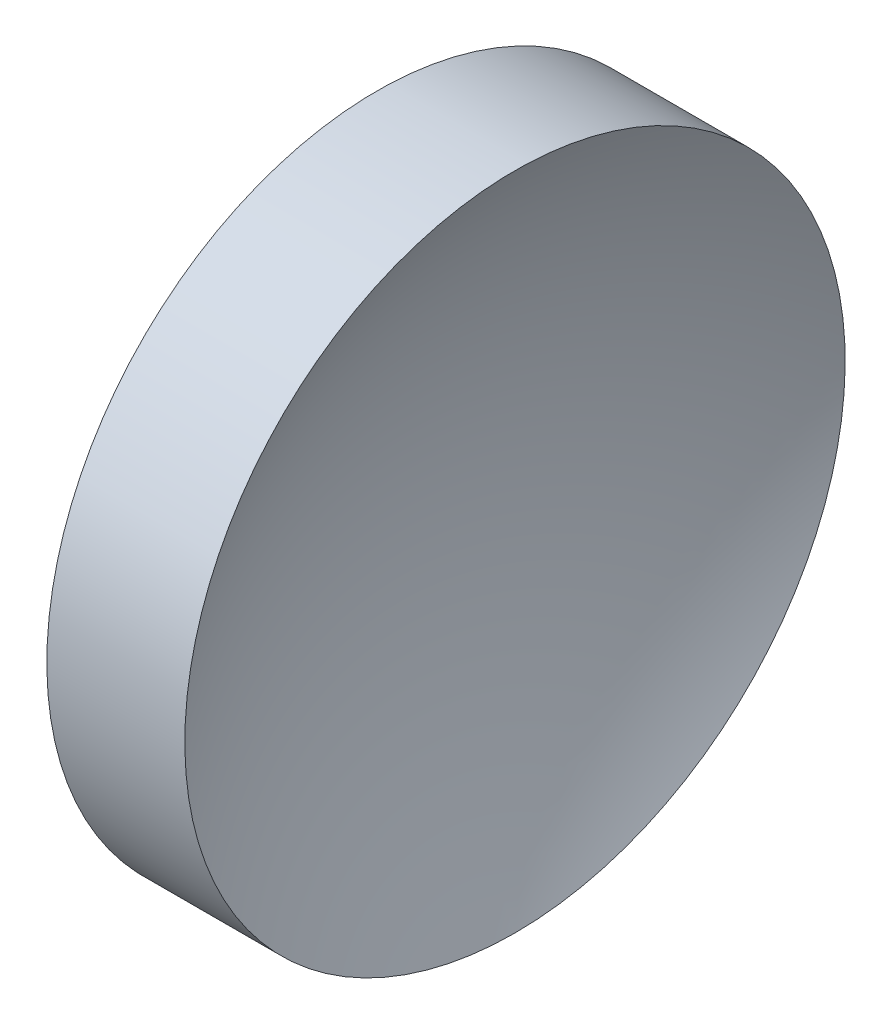
SolidWorks part; units mm, degrees
ref_plane "前视基准面" through (0, 0, 0) normal (0, 0, 1) x (1, 0, 0)
ref_plane "上视基准面" through (0, 0, 0) normal (0, 1, 0) x (1, 0, 0)
ref_plane "右视基准面" through (0, 0, 0) normal (1, 0, 0) x (0, 0, -1)
sketch "草图1" plane through (0, 0, 0) normal (0, 0, 1) x (1, 0, 0)
  line L0 (55.0074, 32.5787) -> (69.3049, 32.5787) construction
  line L1 (57.3582, 32.5787) -> (57.3582, 45.0787)
  line L2 (59.3582, 32.5787) -> (57.3582, 32.5787)
  line L3 (57.3582, 45.0787) -> (62.5828, 45.0787)
  arc A0 (62.5828, 45.0787) -> (59.3582, 32.5787) centre (85.1982, 32.5787) ccw
revolve "旋转1" add sketch "草图1" angle 360 about L0
